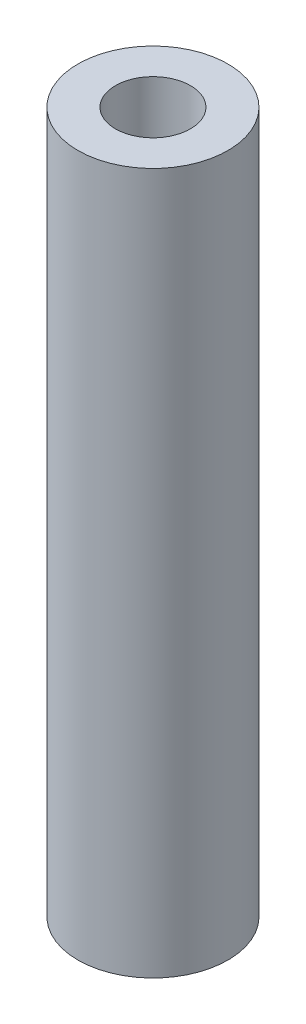
SolidWorks part; units mm, degrees
material "6061-T6 (SS)"
ref_plane "Front" through (0, 0, 0) normal (0, 0, 1) x (1, 0, 0)
ref_plane "Top" through (0, 0, 0) normal (0, 1, 0) x (1, 0, 0)
ref_plane "Right" through (0, 0, 0) normal (1, 0, 0) x (0, 0, -1)
sketch "Sketch1" plane through (0, 0, 0) normal (0, 1, 0) x (1, 0, 0)
  circle A0 centre (0, 0) radius 6.35
  circle A1 centre (0, 0) radius 3.175
  dimension "D1" = 12.7
  dimension "D2" = 6.35
extrude "Boss-Extrude1" add sketch "Sketch1" along normal blind 59.3623
